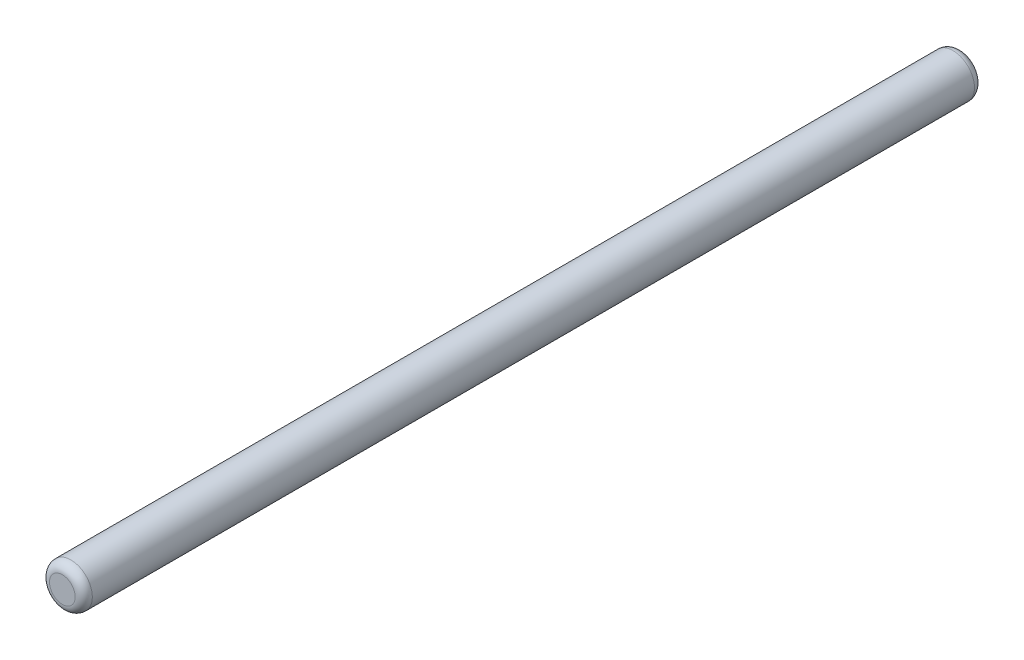
SolidWorks part; units mm, degrees
ref_plane "Plan de face" through (0, 0, 0) normal (0, 0, 1) x (1, 0, 0)
ref_plane "Plan de dessus" through (0, 0, 0) normal (0, 1, 0) x (1, 0, 0)
ref_plane "Plan de droite" through (0, 0, 0) normal (1, 0, 0) x (0, 0, -1)
sketch "Esquisse1" plane through (0, 0, 0) normal (0, 0, 1) x (1, 0, 0)
  circle A0 centre (0, 0) radius 2.5
  dimension "D1" = 5
extrude "Boss.-Extru.1" add sketch "Esquisse1" along normal blind 105
fillet "Congé1" radius 1 2 edges at (2.5, 0, 0) (2.5, 0, 105)
